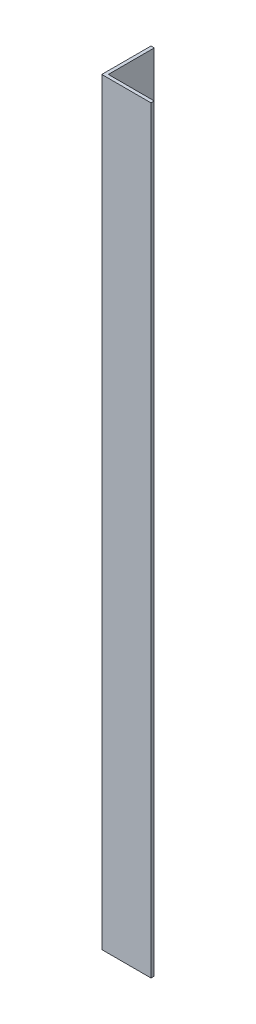
SolidWorks part; units mm, degrees
material "1060 Сплав"
ref_plane "Спереди" through (0, 0, 0) normal (0, 0, 1) x (1, 0, 0)
ref_plane "Сверху" through (0, 0, 0) normal (0, 1, 0) x (1, 0, 0)
ref_plane "Справа" through (0, 0, 0) normal (1, 0, 0) x (0, 0, -1)
sketch "Эскиз1" plane through (0, 0, 0) normal (0, 1, 0) x (1, 0, 0)
  line L0 (0, 0) -> (0, 15)
  line L1 (0, 15) -> (1, 15)
  line L2 (1, 15) -> (1, 1)
  line L3 (1, 1) -> (15, 1)
  line L4 (15, 1) -> (15, 0)
  line L5 (15, 0) -> (0, 0)
  dimension "D1" = 1
  dimension "D2" = 15
extrude "Бобышка-Вытянуть1" add sketch "Эскиз1" along normal blind 231
